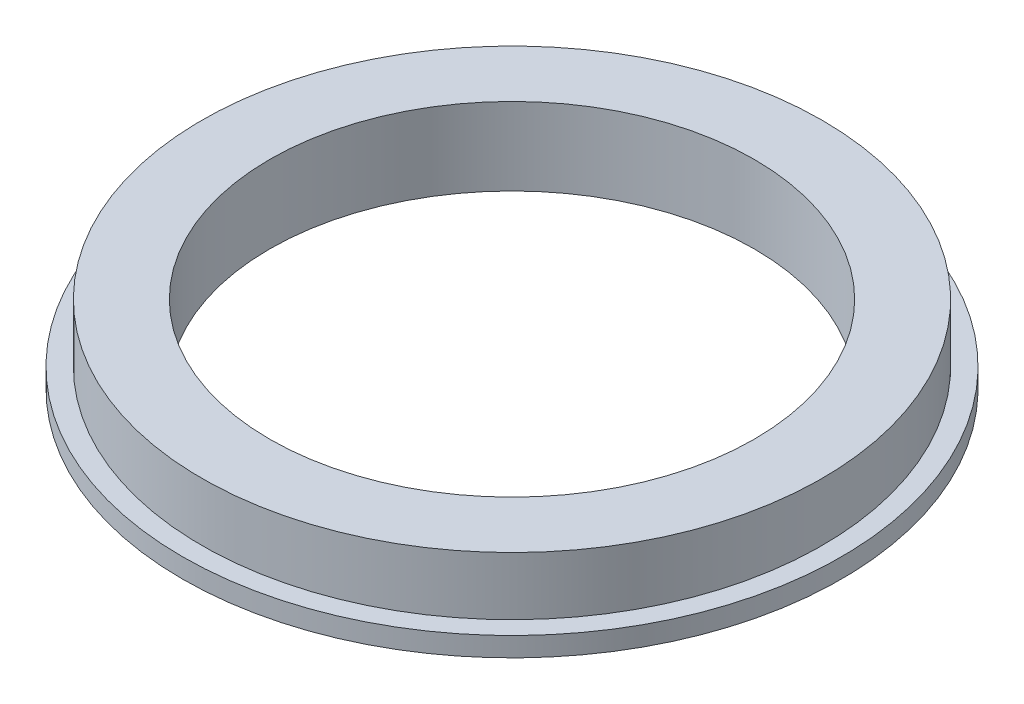
SolidWorks part; units mm, degrees
ref_plane "前视基准面" through (0, 0, 0) normal (0, 0, 1) x (1, 0, 0)
ref_plane "上视基准面" through (0, 0, 0) normal (0, 1, 0) x (1, 0, 0)
ref_plane "右视基准面" through (0, 0, 0) normal (1, 0, 0) x (0, 0, -1)
sketch "草图2" plane through (0, 0, 0) normal (0, 0, 1) x (1, 0, 0)
  line L1 (12.5, 4) -> (16, 4)
  line L2 (16, 4) -> (16, 1)
  line L3 (16, 1) -> (17, 1)
  line L4 (17, 1) -> (17, 0)
  line L5 (17, 0) -> (12.5, 0)
  line L6 (12.5, 4) -> (12.5, 0)
  line L7 (0, -1.2009) -> (0, 5.3458) construction
revolve "旋转1" add sketch "草图2" angle 360 about L7
